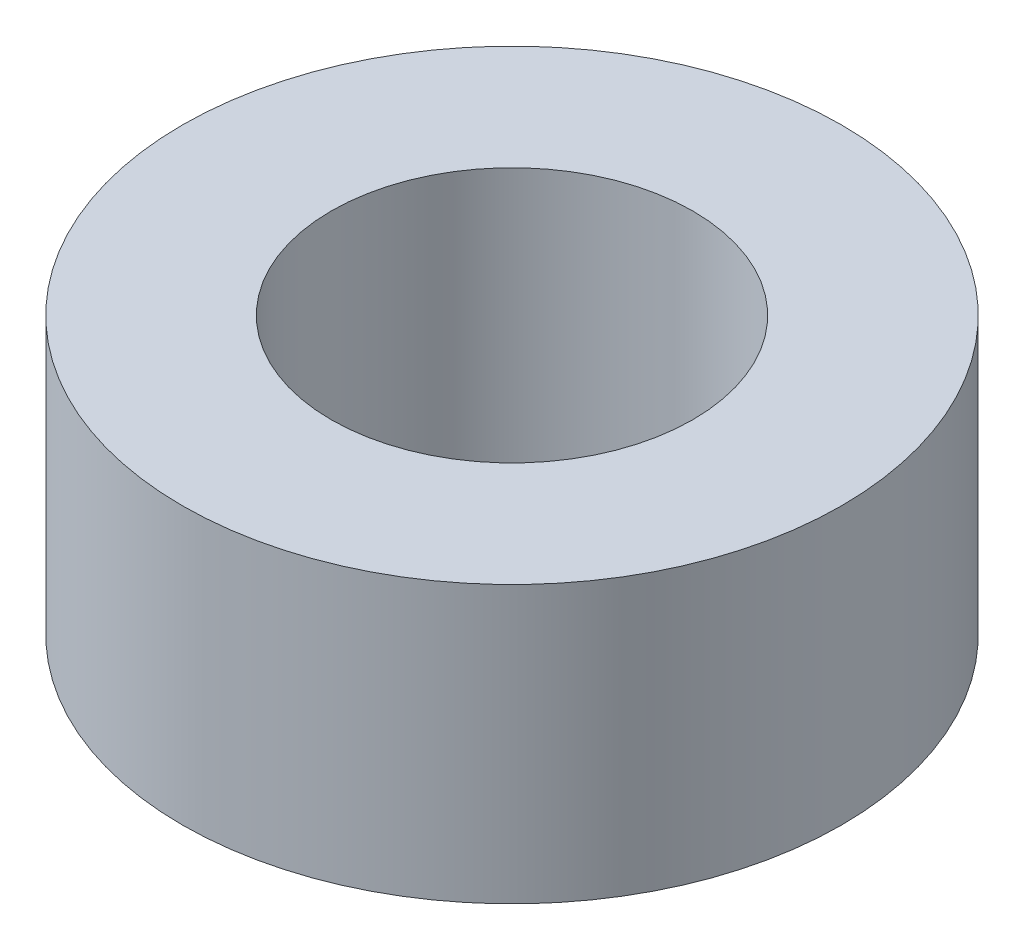
SolidWorks part; units mm, degrees
ref_plane "Front Plane" through (0, 0, 0) normal (0, 0, 1) x (1, 0, 0)
ref_plane "Top Plane" through (0, 0, 0) normal (0, 1, 0) x (1, 0, 0)
ref_plane "Right Plane" through (0, 0, 0) normal (1, 0, 0) x (0, 0, -1)
sketch "Sketch1" plane through (0, 0, 0) normal (0, 1, 0) x (1, 0, 0)
  circle A0 centre (0, 0) radius 1.7
  circle A1 centre (0, 0) radius 3.1
  point P5 (0, -0.0885)
  dimension "D1" = 3.4
  dimension "D2" = 6.2
extrude "Boss-Extrude1" add sketch "Sketch1" along normal mid plane 2.6
